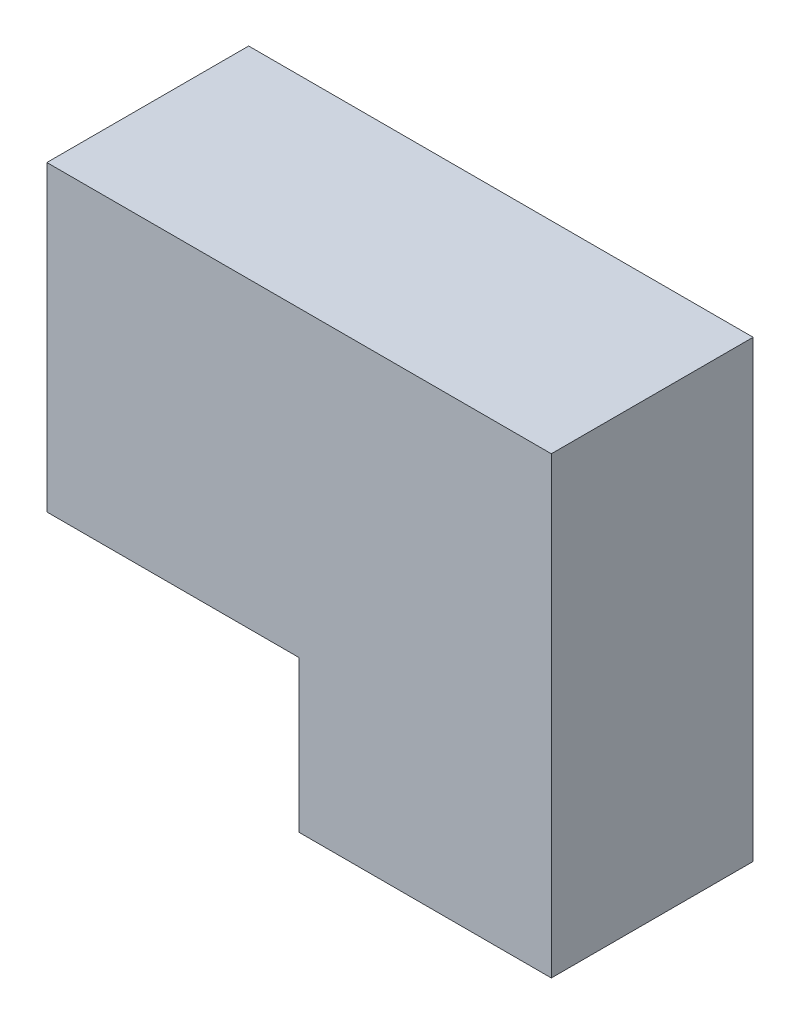
SolidWorks part; units mm, degrees
ref_plane "Front Plane" through (0, 0, 0) normal (0, 0, 1) x (1, 0, 0)
ref_plane "Top Plane" through (0, 0, 0) normal (0, 1, 0) x (1, 0, 0)
ref_plane "Right Plane" through (0, 0, 0) normal (1, 0, 0) x (0, 0, -1)
sketch "Sketch1" plane through (0, 0, 0) normal (0, 0, 1) x (1, 0, 0)
  line L0 (0, 0) -> (0, 3)
  line L1 (0, 3) -> (-5, 3)
  line L2 (-5, 3) -> (-5, 9)
  line L3 (-5, 9) -> (5, 9)
  line L6 (5, 9) -> (5, 0)
  line L7 (5, 0) -> (0, 0)
  dimension "D1" = 5
  dimension "D2" = 3
  dimension "D3" = 9
extrude "Boss-Extrude1" add sketch "Sketch1" along normal blind 4
